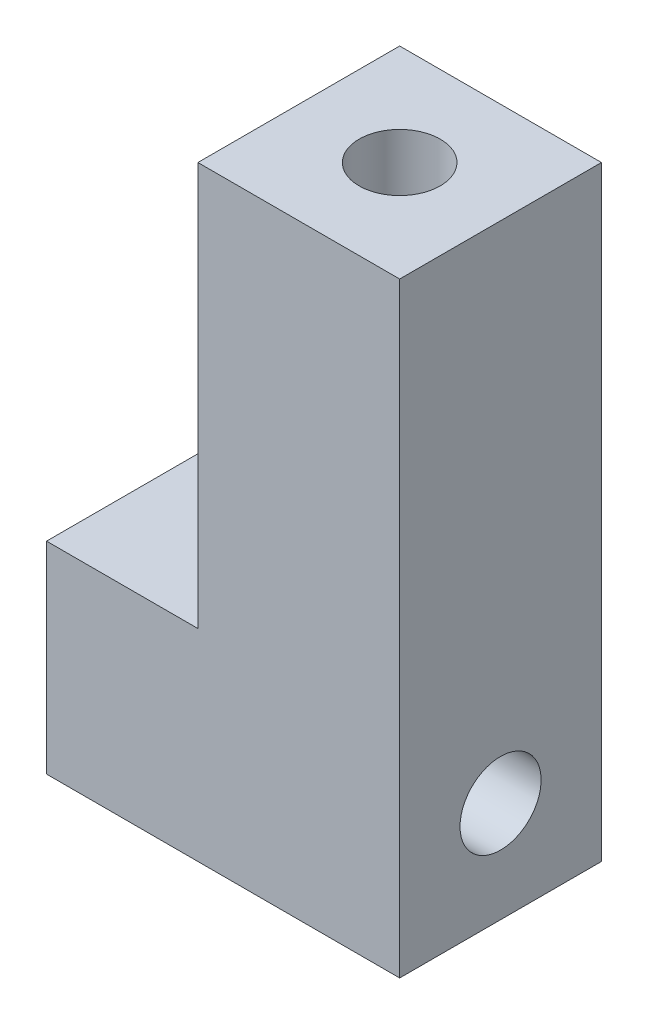
SolidWorks part; units mm, degrees
material "6061-T6 (SS)"
ref_plane "Front" through (0, 0, 0) normal (0, 0, 1) x (1, 0, 0)
ref_plane "Top" through (0, 0, 0) normal (0, 1, 0) x (1, 0, 0)
ref_plane "Right" through (0, 0, 0) normal (1, 0, 0) x (0, 0, -1)
sketch "Sketch1" plane through (0, 0, 0) normal (0, 0, 1) x (1, 0, 0)
  line L0 (0, 0) -> (0, 38.1)
  line L1 (0, 38.1) -> (-12.7, 38.1)
  line L2 (-12.7, 38.1) -> (-12.7, 12.7)
  line L3 (-12.7, 12.7) -> (-22.225, 12.7)
  line L4 (-22.225, 12.7) -> (-22.225, 0)
  line L5 (-22.225, 0) -> (0, 0)
  dimension "D1" = 12.7
  dimension "D2" = 12.7
  dimension "D3" = 38.1
  dimension "D4" = 22.225
extrude "Boss-Extrude1" add sketch "Sketch1" along normal blind 12.7
hole_wizard "1/4-20 Tapped Hole1" positions "Sketch2" profile "Sketch3" tap size "1/4-20" standard "ANSI Inch" end condition through all
sketch "Sketch2" plane through (0, 38.1, 0) normal (0, 1, 0) x (1, 0, 0)
  line L0 (-12.7, 0) -> (0, -12.7) construction
  point P0 (-6.35, -6.35)
sketch "Sketch3" plane through (-6.35, 38.1, 6.35) normal (1, 0, 0) x (0, 0, 1)
  line L0 (0, 0) -> (0, 38.1)
  line L1 (0, 38.1) -> (2.5527, 38.1)
  line L2 (2.5527, 38.1) -> (2.5527, 0)
  line L5 (2.5527, 0) -> (0, 0)
  line L11 (0, -6.35) -> (0, 107.95) construction
  dimension "Thru Tap Drill Dia." = 5.1054
  dimension "Thru Tap Drill Depth" = 38.1
cosmetic thread "Hole Thread1" parameters "D2"=6.35
hole_wizard "1/4-20 Tapped Hole2" positions "Sketch4" profile "Sketch5" tap size "1/4-20" standard "ANSI Inch" end condition through all
sketch "Sketch4" plane through (-22.225, 0, 0) normal (-1, 0, 0) x (0, 0, 1)
  line L0 (0, 12.7) -> (12.7, 0) construction
  point P0 (6.35, 6.35)
cosmetic thread "Hole Thread2" parameters "D2"=6.35
sketch "Sketch5" plane through (-22.225, 6.35, 6.35) normal (0, 1, 0) x (0, 0, 1)
  line L0 (0, 0) -> (0, 22.225)
  line L1 (0, 22.225) -> (2.5527, 22.225)
  line L2 (2.5527, 22.225) -> (2.5527, 0)
  line L5 (2.5527, 0) -> (0, 0)
  line L11 (0, -6.35) -> (0, 107.95) construction
  dimension "Thru Tap Drill Dia." = 5.1054
  dimension "Thru Tap Drill Depth" = 22.225
